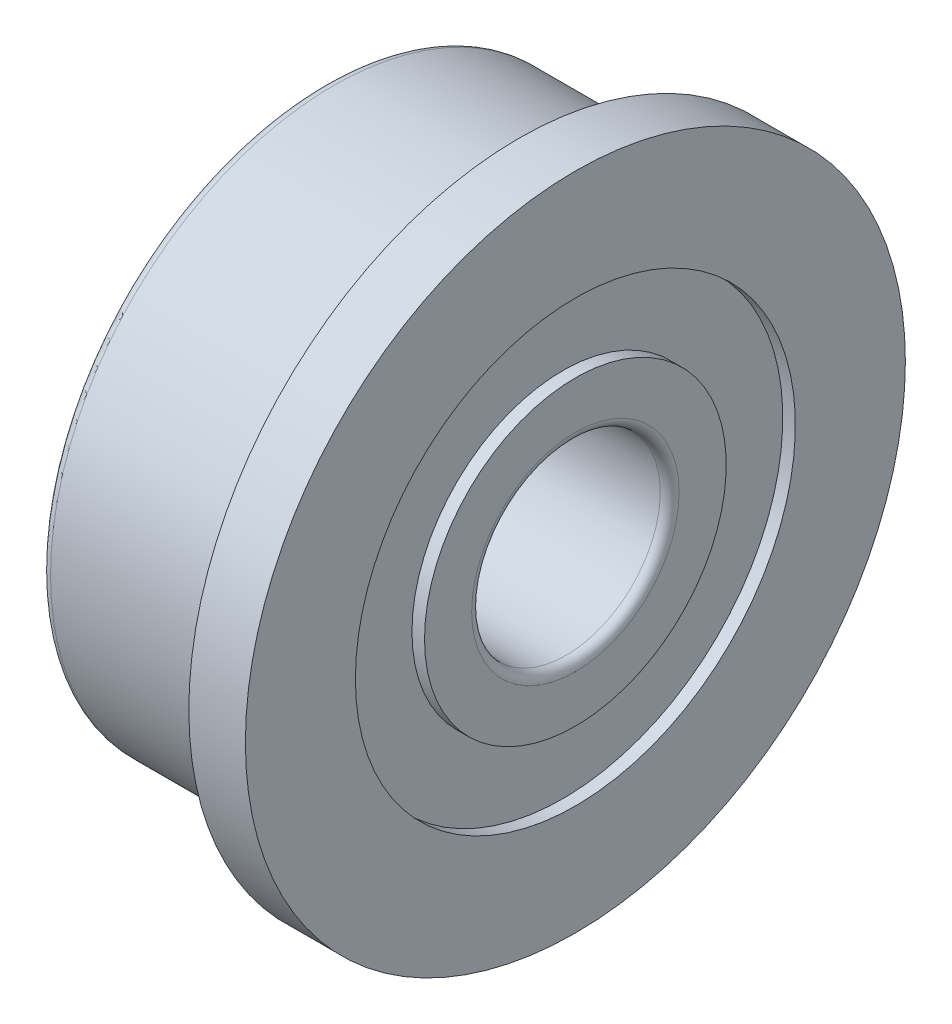
SolidWorks part; units mm, degrees
ref_plane "Front Plane" through (0, 0, 0) normal (0, 0, 1) x (1, 0, 0)
ref_plane "Top Plane" through (0, 0, 0) normal (0, 1, 0) x (1, 0, 0)
ref_plane "Right Plane" through (0, 0, 0) normal (1, 0, 0) x (0, 0, -1)
sketch "Sketch1" plane through (0, 0, 0) normal (0, 0, 1) x (1, 0, 0)
  line L0 (-3.1, 0) -> (0.9, 0) construction
  line L1 (0, 4.7) -> (0, 5.25)
  line L2 (0, 5.25) -> (0.9, 5.25)
  line L3 (0.9, 5.25) -> (0.9, 3.5)
  line L4 (0.9, 1.5) -> (-3.1, 1.5)
  line L5 (-3.1, 1.5) -> (-3.1, 2.4)
  line L6 (-3.1, 4.5) -> (-0.2, 4.5)
  line L7 (-3.1, 3.5) -> (-2.9, 3.5)
  line L8 (-2.9, 3.5) -> (-2.9, 2.4)
  line L9 (-2.9, 2.4) -> (-3.1, 2.4)
  line L10 (0.9, 3.5) -> (0.7, 3.5)
  line L11 (0.7, 3.5) -> (0.7, 2.4)
  line L12 (0.7, 2.4) -> (0.9, 2.4)
  line L13 (-3.1, 3.5) -> (-3.1, 4.5)
  line L14 (0.9, 2.4) -> (0.9, 1.5)
  arc A0 (-0.2, 4.5) -> (0, 4.7) centre (0, 4.5) ccw
  dimension "FIX_1" = 0.2
  dimension "D_s" = 3
  dimension "C" = 0.9
  dimension "MSM_2" = 4.8
  dimension "MSM_1" = 7
  dimension "D" = 9
  dimension "D1." = 10.5
  dimension "B" = 4
  dimension "MSM_3" = 0.2
revolve "Revolve1" add sketch "Sketch1" angle 360 about L0
fillet "Fillet1" radius 0.15 3 edges at (0.9, 0, 1.5) (-3.1, 0, 1.5) (-3.1, 0, 4.5)
